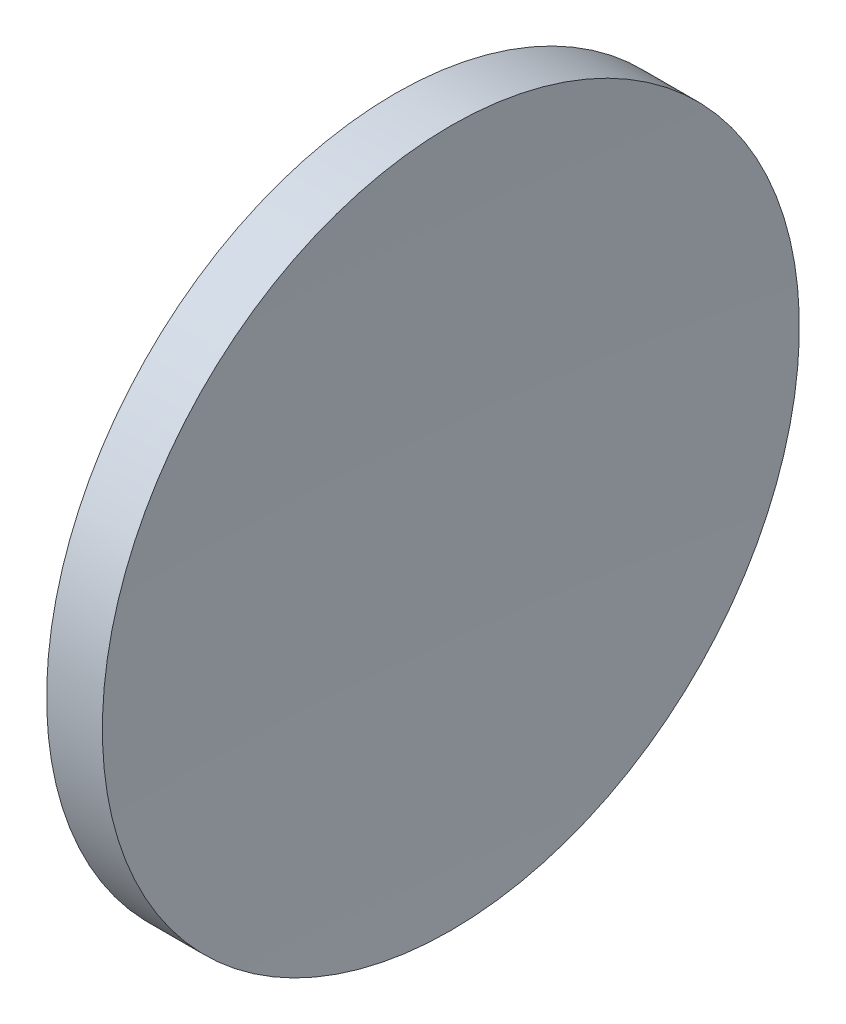
SolidWorks part; units mm, degrees
ref_plane "前视基准面" through (0, 0, 0) normal (0, 0, 1) x (1, 0, 0)
ref_plane "上视基准面" through (0, 0, 0) normal (0, 1, 0) x (1, 0, 0)
ref_plane "右视基准面" through (0, 0, 0) normal (1, 0, 0) x (0, 0, -1)
sketch "草图1" plane through (0, 0, 0) normal (0, 0, 1) x (1, 0, 0)
  line L0 (115.9445, 65.2168) -> (135.9482, 65.2168) construction
  line L1 (124.1897, 84.2418) -> (127.232, 84.2418)
  line L2 (126.7554, 65.2168) -> (122.8554, 65.2168)
  arc A0 (124.1897, 84.2418) -> (122.8554, 65.2168) centre (259.1554, 65.2168) ccw
  arc A1 (127.232, 84.2418) -> (126.7554, 65.2168) centre (506.7554, 65.2168) ccw
revolve "旋转1" add sketch "草图1" angle 360 about L0
